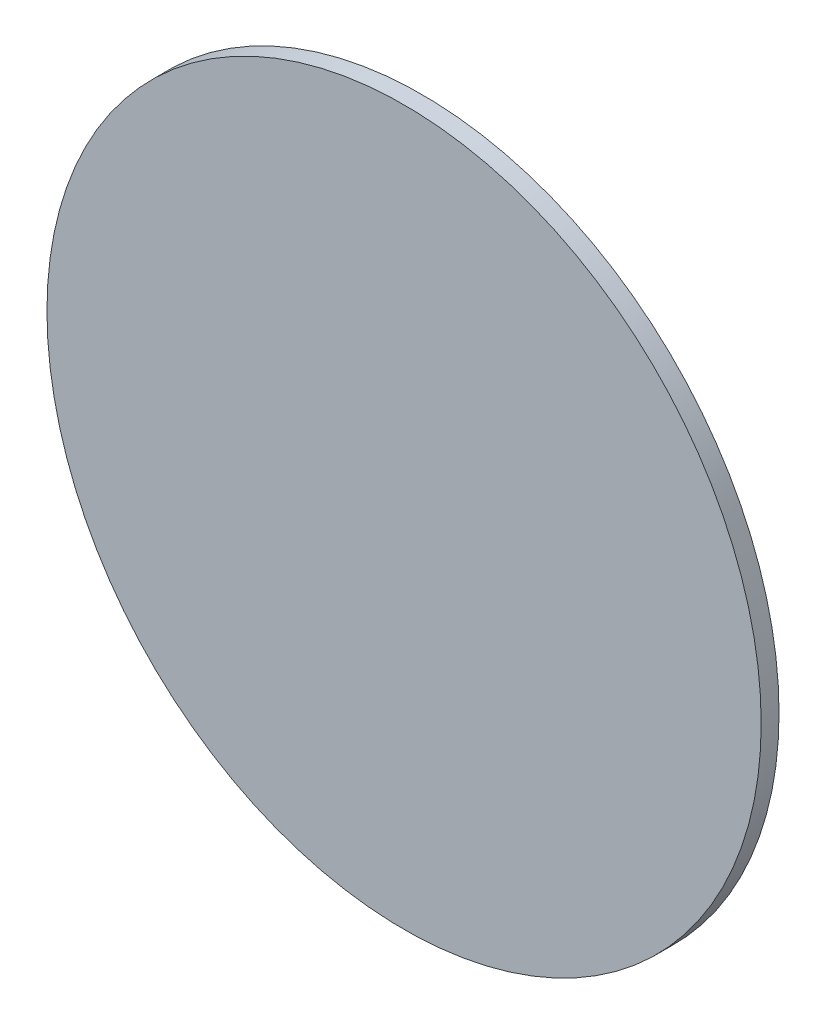
SolidWorks part; units mm, degrees
ref_plane "Front Plane" through (0, 0, 0) normal (0, 0, 1) x (1, 0, 0)
ref_plane "Top Plane" through (0, 0, 0) normal (0, 1, 0) x (1, 0, 0)
ref_plane "Right Plane" through (0, 0, 0) normal (1, 0, 0) x (0, 0, -1)
sketch "Sketch1" plane through (0, 0, 0) normal (0, 0, 1) x (1, 0, 0)
  circle A0 centre (0, 0) radius 60
  dimension "D1" = 120
extrude "Boss-Extrude1" add sketch "Sketch1" along normal blind 3
